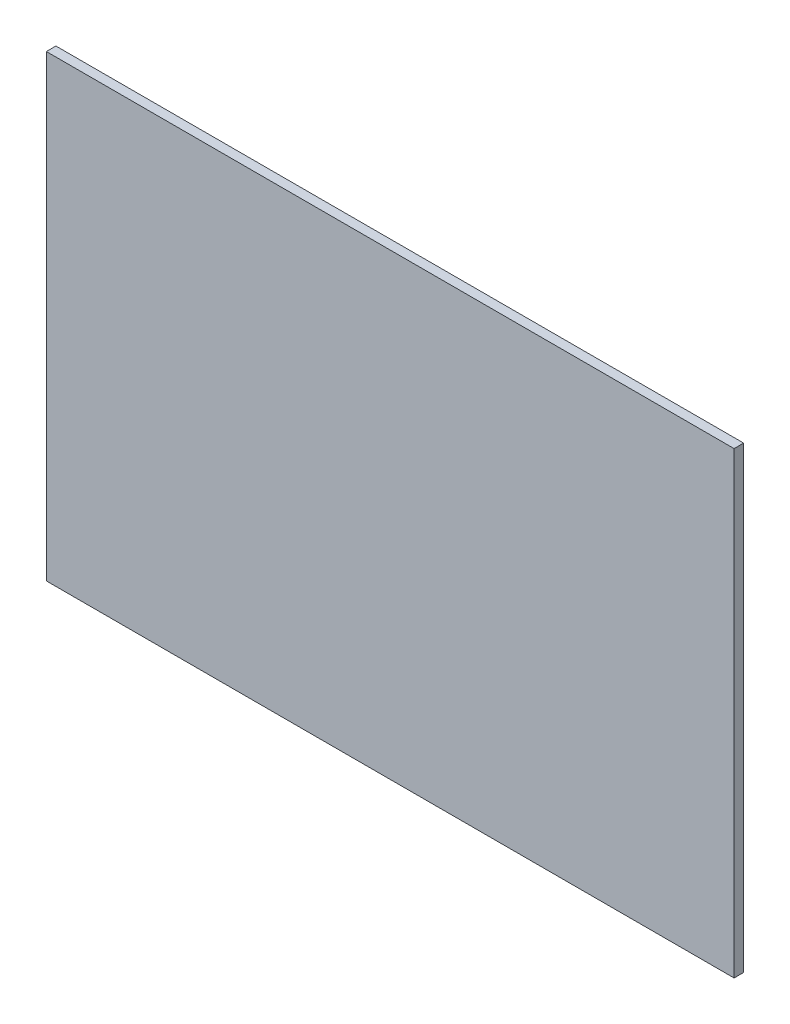
SolidWorks part; units mm, degrees
ref_plane "Front Plane" through (0, 0, 0) normal (0, 0, 1) x (1, 0, 0)
ref_plane "Top Plane" through (0, 0, 0) normal (0, 1, 0) x (1, 0, 0)
ref_plane "Right Plane" through (0, 0, 0) normal (1, 0, 0) x (0, 0, -1)
sketch "Sketch1" plane through (0, 0, 0) normal (0, 0, 1) x (1, 0, 0)
  line L1 (0, 0) -> (1828.8, 0)
  line L2 (0, 0) -> (0, -1219.2)
  line L3 (0, -1219.2) -> (1828.8, -1219.2)
  line L4 (1828.8, 0) -> (1828.8, -1219.2)
  dimension "D1" = 1219.2
  dimension "D2" = 1828.8
extrude "Boss-Extrude1" add sketch "Sketch1" along normal blind 25.4
